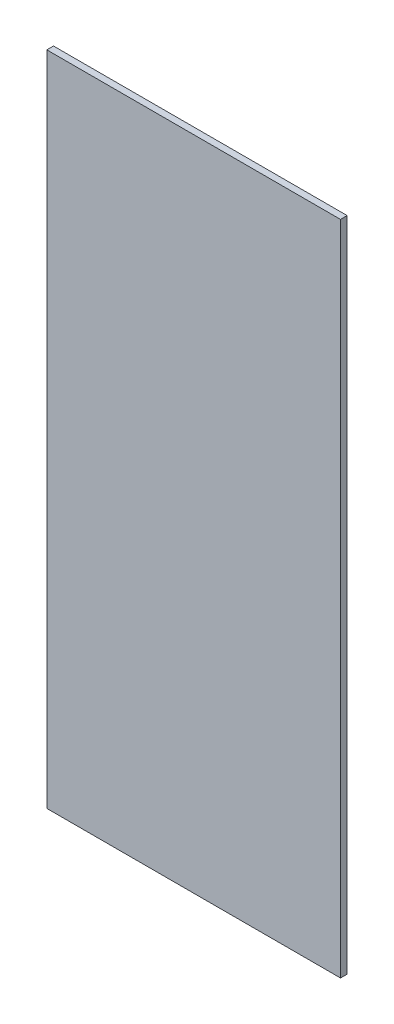
SolidWorks part; units mm, degrees
ref_plane "Спереди" through (0, 0, 0) normal (0, 0, 1) x (1, 0, 0)
ref_plane "Сверху" through (0, 0, 0) normal (0, 1, 0) x (1, 0, 0)
ref_plane "Справа" through (0, 0, 0) normal (1, 0, 0) x (0, 0, -1)
sketch "Sketch1" plane through (0, 0, 0) normal (0, 0, 1) x (1, 0, 0)
  line L0 (88.2, 0) -> (88.2, -394.6) construction
  line L1 (-88.2, 0) -> (88.2, 0)
  line L2 (-88.2, 0) -> (-88.2, -394.6)
  line L3 (-88.2, -394.6) -> (88.2, -394.6)
  line L4 (88.2, 0) -> (88.2, -394.6)
  line L7 (88.2, -394.6) -> (84.2, -394.6) construction
  point P4 (0, -394.6)
  point P5 (0, 0)
extrude "Extrude1" add sketch "Sketch1" along normal blind 4
equation "\"thickness\"=4"
equation "\"D1@Extrude1\"=\"thickness\""
equation "\"pin_l\"=5"
equation "\"pin_skew\"=4"
equation "\"pin_r\"=5"
equation "\"M4_plastic_thread\"=3.8"
equation "\"M3_plastic_thread\" = 2.8"
